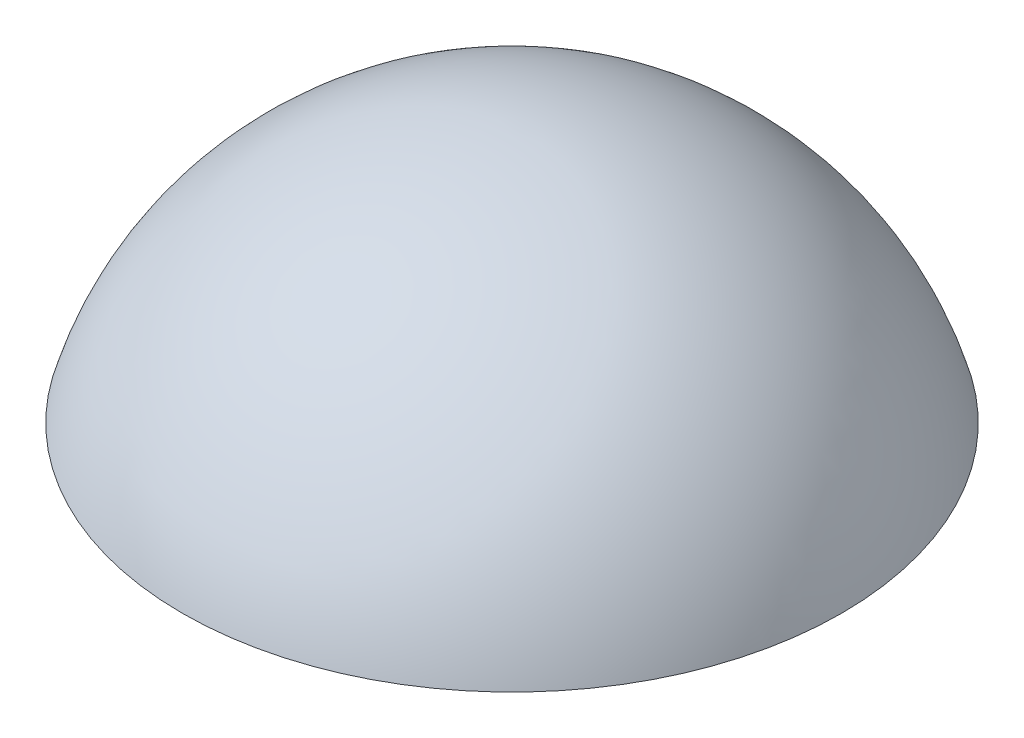
SolidWorks part; units mm, degrees
ref_plane "Front Plane" through (0, 0, 0) normal (0, 0, 1) x (1, 0, 0)
ref_plane "Top Plane" through (0, 0, 0) normal (0, 1, 0) x (1, 0, 0)
ref_plane "Right Plane" through (0, 0, 0) normal (1, 0, 0) x (0, 0, -1)
sketch "Sketch1" plane through (0, 0, 0) normal (0, 0, 1) x (1, 0, 0)
  line L0 (0, 0) -> (0, 5.2292) construction
  line L1 (0, 0) -> (-3.5, 0)
  line L2 (-5.6535, 2.65) -> (4.3394, 2.65) construction
  line L3 (0, 2.65) -> (0, 0)
  arc A0 (0, 2.65) -> (-3.5, 0) centre (0, -0.9863) ccw
  point P6 (-3.5, 0)
  dimension "D1" = 7
  dimension "D2" = 2.65
revolve "Revolve1" add sketch "Sketch1" angle 360 about L0
